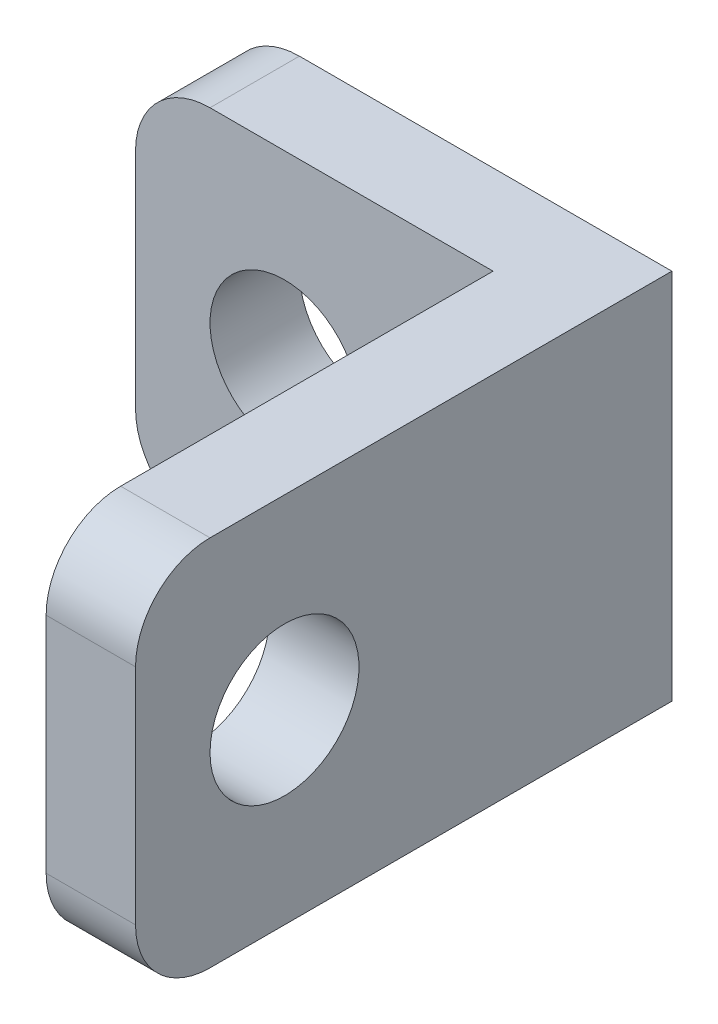
SolidWorks part; units mm, degrees
ref_plane "Front" through (0, 0, 0) normal (0, 0, 1) x (1, 0, 0)
ref_plane "Top" through (0, 0, 0) normal (0, 1, 0) x (1, 0, 0)
ref_plane "Right" through (0, 0, 0) normal (1, 0, 0) x (0, 0, -1)
sketch "草图1" plane through (0, 0, 0) normal (0, 0, 1) x (1, 0, 0)
  line L3 (1, 0) -> (6, 0)
  line L4 (0, 1) -> (0, 4)
  line L5 (1, 5) -> (6, 5)
  line L6 (6, 0) -> (6, 5)
  circle A2 centre (2, 2.5) radius 1
  arc A3 (0, 4) -> (1, 5) centre (1, 4) cw
  arc A4 (1, 0) -> (0, 1) centre (1, 1) cw
  point P13 (0, 0)
  dimension "D1" = 1
  dimension "D2" = 1
  dimension "D3" = 2
  dimension "D5" = 2.5
  dimension "D4" = 2.5
  dimension "D6" = 4
extrude "凸台-拉伸1" add sketch "草图1" along normal blind 1.2
sketch "草图2" plane through (0, 0, 1.2) normal (0, 0, -1) x (-1, 0, 0)
  line L0 (-6, 0) -> (-6, 5) construction
  line L1 (-4.8, 0) -> (-6, 0)
  line L2 (-4.8, 0) -> (-4.8, 5)
  line L3 (-4.8, 5) -> (-6, 5)
  line L4 (-6, 0) -> (-6, 5)
  line L5 (-6, 5) -> (-1, 5) construction
  dimension "D1" = 0
  dimension "D2" = 1.2
  dimension "D3" = 0
extrude "凸台-拉伸2" add sketch "草图2" against normal blind 6
fillet "圆角1" radius 1 2 edges at (5.4, 0, 7.2) (5.4, 5, 7.2)
sketch "草图4" plane through (4.8, 0, 0) normal (-1, 0, 0) x (0, 0, 1)
  line L2 (7.2, 1) -> (7.2, 4) construction
  circle A0 centre (5.2, 2.5) radius 1
  dimension "D1" = 2
extrude "切除-拉伸1" cut sketch "草图4" against normal blind 2
